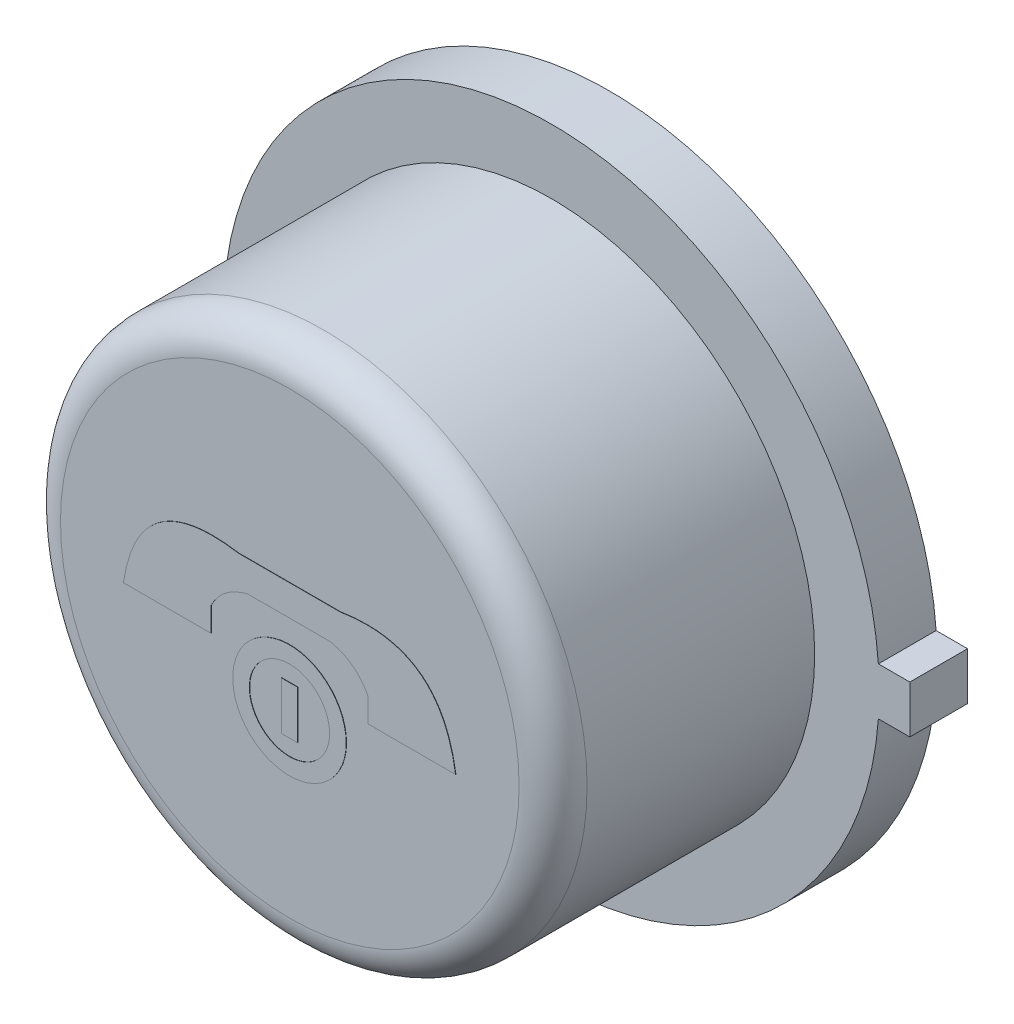
SolidWorks part; units mm, degrees
ref_plane "Front Plane" through (0, 0, 0) normal (0, 0, 1) x (1, 0, 0)
ref_plane "Top Plane" through (0, 0, 0) normal (0, 1, 0) x (1, 0, 0)
ref_plane "Right Plane" through (0, 0, 0) normal (1, 0, 0) x (0, 0, -1)
sketch "Sketch1" plane through (0, 0, 0) normal (0, 0, 1) x (1, 0, 0)
  line L1 (2.4511, 0.1778) -> (2.6797, 0.1778)
  line L3 (2.4511, -0.1778) -> (2.6797, -0.1778)
  line L4 (2.6797, 0.1778) -> (2.6797, -0.1778)
  line L5 (2.4511, 0.1778) -> (2.4444, 0.1778)
  line L6 (2.4511, -0.1778) -> (2.4446, -0.1778)
  arc A0 (2.4446, 0.1778) -> (2.4446, -0.1778) centre (0, 0) ccw
  dimension "D1" = 4.9022
  dimension "D2" = 0.3556
  dimension "D3" = 0.2286
extrude "Boss-Extrude1" add sketch "Sketch1" along normal blind 0.4318
sketch "Sketch2" plane through (0, 0, 0.4318) normal (0, 0, 1) x (1, 0, 0)
  circle A0 centre (0, 0) radius 1.9685
  dimension "D1" = 3.937
extrude "Boss-Extrude2" add sketch "Sketch2" along normal blind 1.9558
sketch "Sketch3" plane through (0, 0, 0) normal (0, 0, -1) x (-1, 0, 0)
  circle A0 centre (0, 0) radius 1.7576
extrude "Boss-Extrude3" add sketch "Sketch3" along normal blind 0.0025
fillet "Fillet1" radius 0.254 1 edges at (1.9685, 0, 2.3876)
sketch "Sketch4" plane through (0, 0, 2.3876) normal (0, 0, 1) x (1, 0, 0)
  line L0 (0, 1.7145) -> (0, -1.7145) construction
  line L1 (-1.242, -0.1605) -> (-0.5862, -0.1605)
  line L2 (-0.5862, -0.1605) -> (-0.5862, 0.0211)
  line L3 (-0.3091, 0.2313) -> (0.3091, 0.2313)
  line L4 (-0.3796, 0.4607) -> (0.3796, 0.4607)
  line L5 (1.242, -0.1605) -> (0.5862, -0.1605)
  line L6 (0.5862, -0.1605) -> (0.5862, 0.0211)
  line L8 (-0.0607, -0.186) -> (0.0607, -0.186)
  line L9 (-0.0607, -0.186) -> (-0.0607, -0.5461)
  line L10 (-0.0607, -0.5461) -> (0.0607, -0.5461)
  line L11 (0.0607, -0.186) -> (0.0607, -0.5461)
  line L12 (-0.0607, -0.186) -> (0.0607, -0.5461) construction
  line L13 (-0.0607, -0.5461) -> (0.0607, -0.186) construction
  circle A1 centre (0, 0) radius 1.7145 construction
  circle A2 centre (0, -0.366) radius 0.4243
  circle A3 centre (0, -0.366) radius 0.3
  spline S0 degree 2 poles (-1.242, -0.1605) (-1.131, 0.5804) (-0.3796, 0.4607) knots 0 0 0 1 1 1
  spline S1 degree 2 poles (-0.5862, 0.0211) (-0.5007, 0.1876) (-0.3091, 0.2313) knots 0 0 0 1 1 1
  spline S2 degree 2 poles (1.242, -0.1605) (1.131, 0.5804) (0.3796, 0.4607) knots 0 0 0 1 1 1
  spline S3 degree 2 poles (0.5862, 0.0211) (0.5007, 0.1876) (0.3091, 0.2313) knots 0 0 0 1 1 1
  point P15 (0, 0.2313)
  point P16 (0, 0.4607)
extrude "Boss-Extrude6" add sketch "Sketch4" along normal blind 0.0025 contours A2 A3 | L11 L8 L9 L10 | S3 L6 L5 S2 L4 S0 L1 L2 S1 L3
